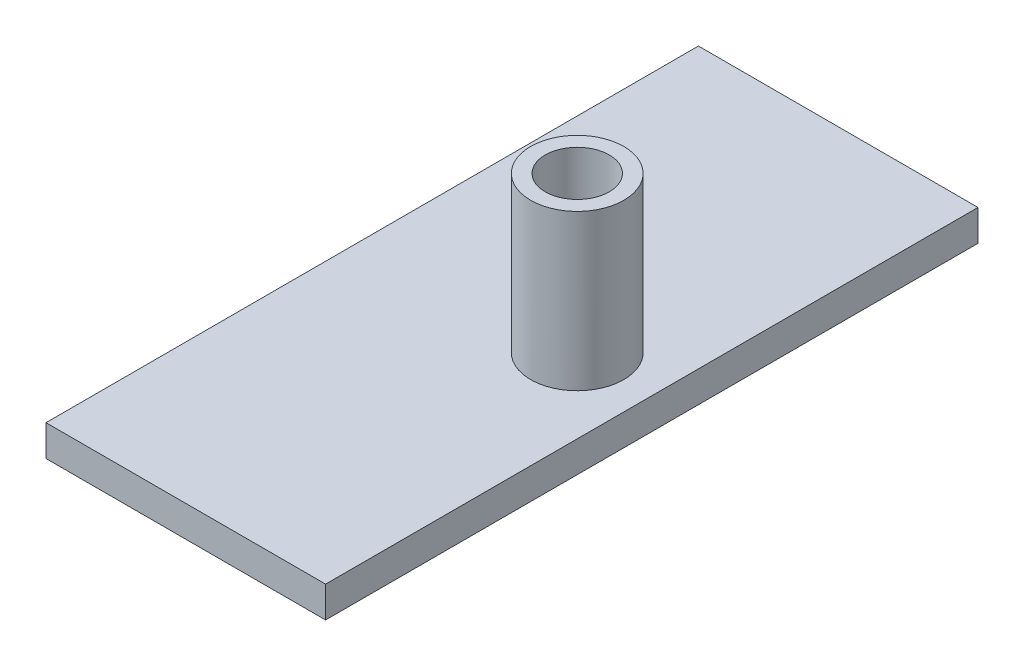
SolidWorks part; units mm, degrees
ref_plane "Front Plane" through (0, 0, 0) normal (0, 0, 1) x (1, 0, 0)
ref_plane "Top Plane" through (0, 0, 0) normal (0, 1, 0) x (1, 0, 0)
ref_plane "Right Plane" through (0, 0, 0) normal (1, 0, 0) x (0, 0, -1)
sketch "Sketch1" plane through (0, 0, 0) normal (0, 1, 0) x (1, 0, 0)
  line L1 (0, 0) -> (45, 0)
  line L2 (0, 0) -> (0, 105)
  line L3 (0, 105) -> (45, 105)
  line L4 (45, 0) -> (45, 105)
  point P5 (0, 0)
extrude "Boss-Extrude3" add sketch "Sketch1" along normal blind 5 contours L1 L4 L3 L2
sketch "Sketch3" plane through (0, 5, 0) normal (0, 1, 0) x (1, 0, 0)
  circle A0 centre (33, 52.5) radius 7.5
  point P2 (0, 0)
  point P3 (0, 0)
extrude "Boss-Extrude4" add sketch "Sketch3" along normal blind 25
sketch "Sketch4" plane through (0, 30, 0) normal (0, 1, 0) x (1, 0, 0)
  circle A0 centre (33, 52.5) radius 5.15
  point P3 (0, 0)
extrude "Cut-Extrude1" cut sketch "Sketch4" against normal blind 20
